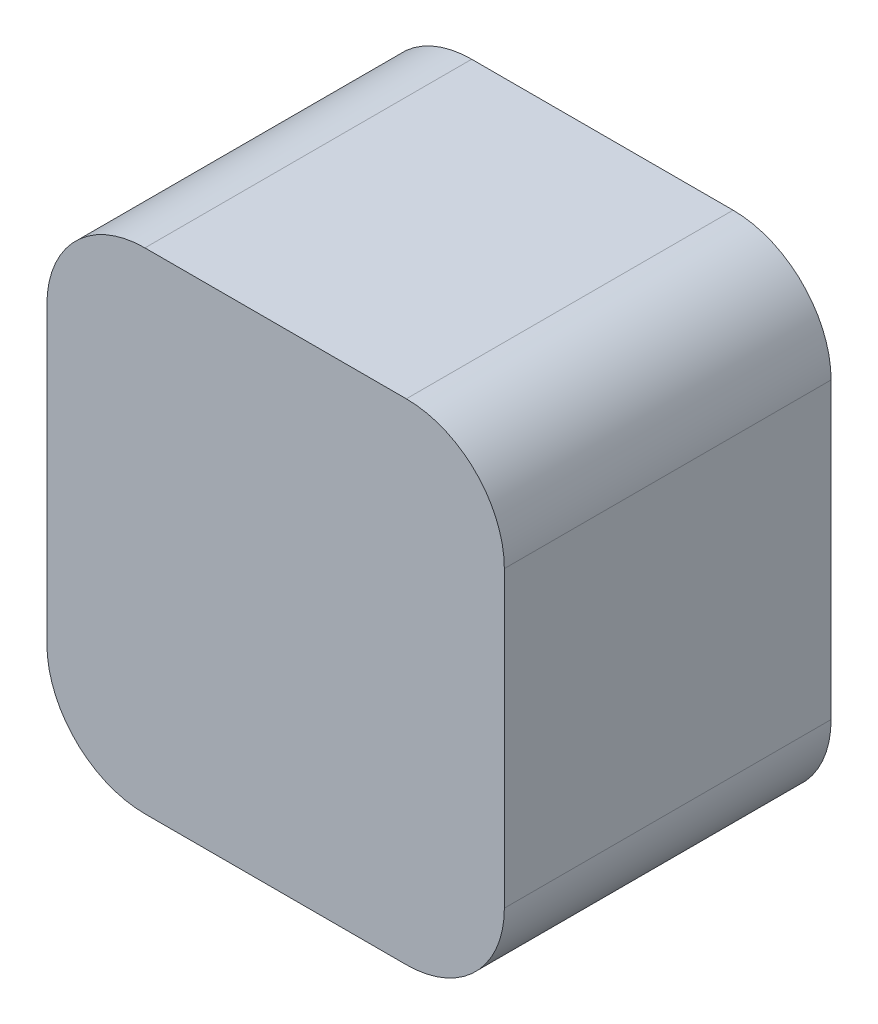
SolidWorks part; units mm, degrees
ref_plane "Front Plane" through (0, 0, 0) normal (0, 0, 1) x (1, 0, 0)
ref_plane "Top Plane" through (0, 0, 0) normal (0, 1, 0) x (1, 0, 0)
ref_plane "Right Plane" through (0, 0, 0) normal (1, 0, 0) x (0, 0, -1)
sketch "Sketch1" plane through (0, 0, 0) normal (0, 0, 1) x (1, 0, 0)
  line L1 (0, 0) -> (14, 0)
  line L2 (0, 0) -> (0, 15)
  line L3 (0, 15) -> (14, 15)
  line L4 (14, 0) -> (14, 15)
  dimension "D1" = 14
  dimension "D2" = 15
extrude "Boss-Extrude1" add sketch "Sketch1" along normal blind 10
fillet "Fillet1" radius 3 4 edges at (0, 0, 5) (14, 0, 5) (0, 15, 5) (14, 15, 5)
